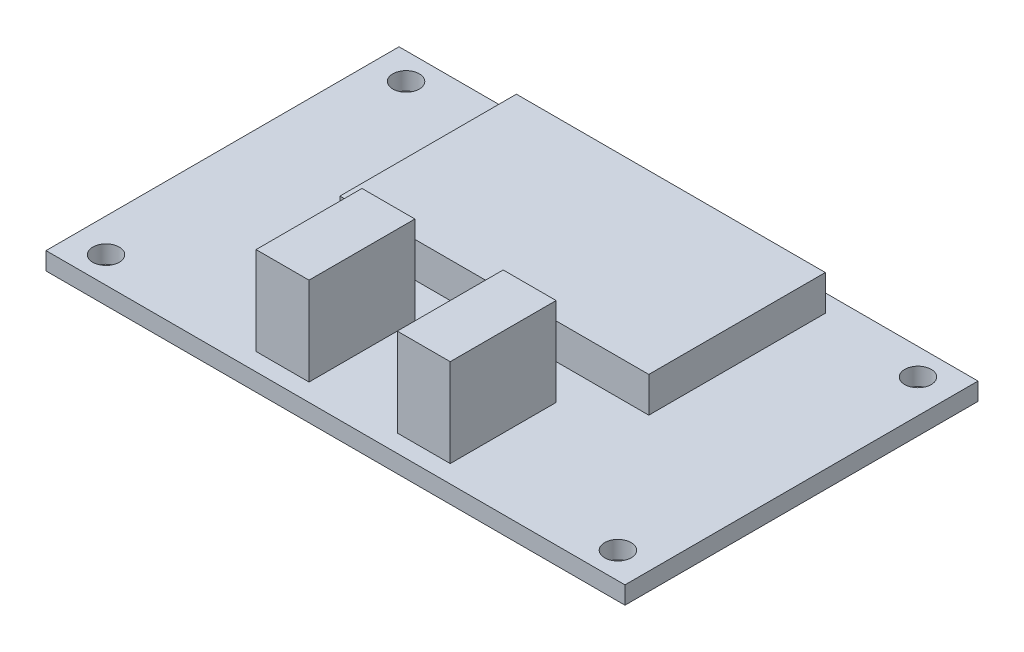
SolidWorks part; units mm, degrees
ref_plane "Front" through (0, 0, 0) normal (0, 0, 1) x (1, 0, 0)
ref_plane "Top" through (0, 0, 0) normal (0, 1, 0) x (1, 0, 0)
ref_plane "Right" through (0, 0, 0) normal (1, 0, 0) x (0, 0, -1)
sketch "Sketch1" plane through (0, 0, 0) normal (0, 1, 0) x (1, 0, 0)
  line L1 (-32.8, -20) -> (32.8, -20)
  line L2 (-32.8, -20) -> (-32.8, 20)
  line L3 (-32.8, 20) -> (32.8, 20)
  line L4 (32.8, -20) -> (32.8, 20)
  line L5 (-32.8, -20) -> (32.8, 20) construction
  line L6 (-32.8, 20) -> (32.8, -20) construction
  point P0 (0, 0)
  dimension "D1" = 65.6
  dimension "D2" = 40
extrude "Boss-Extrude1" add sketch "Sketch1" along normal blind 2
sketch "Sketch2" plane through (0, 2, 0) normal (0, 1, 0) x (1, 0, 0)
  line L1 (-29, -17) -> (29, -17) construction
  line L2 (-29, -17) -> (-29, 17) construction
  line L3 (-29, 17) -> (29, 17) construction
  line L4 (29, -17) -> (29, 17) construction
  line L5 (-29, -17) -> (29, 17) construction
  line L6 (-29, 17) -> (29, -17) construction
  circle A0 centre (-29, 17) radius 1.5
  circle A1 centre (29, 17) radius 1.5
  circle A2 centre (29, -17) radius 1.5
  circle A3 centre (-29, -17) radius 1.5
  point P0 (0, 0)
  dimension "D3" = 3
  dimension "D1" = 58
  dimension "D2" = 34
extrude "Cut-Extrude1" cut sketch "Sketch2" against normal through all
sketch "Sketch3" plane through (0, 2, 0) normal (0, 1, 0) x (1, 0, 0)
  line L0 (32.8, 20) -> (-32.8, 20) construction
  line L1 (-17.5, -2) -> (17.5, -2)
  line L2 (-17.5, -2) -> (-17.5, 18)
  line L3 (-17.5, 18) -> (17.5, 18)
  line L4 (17.5, -2) -> (17.5, 18)
  line L5 (-17.5, -2) -> (17.5, 18) construction
  line L6 (-17.5, 18) -> (17.5, -2) construction
  line L7 (0, 8) -> (0, 0) construction
  point P0 (0, 8)
  dimension "D1" = 20
  dimension "D2" = 35
  dimension "D3" = 2
extrude "Boss-Extrude2" add sketch "Sketch3" along normal blind 4
sketch "Sketch4" plane through (0, 2, 0) normal (0, 1, 0) x (1, 0, 0)
  line L0 (-32.8, -20) -> (32.8, -20) construction
  line L1 (-11, -18) -> (-5, -18)
  line L2 (-11, -18) -> (-11, -6)
  line L3 (-11, -6) -> (-5, -6)
  line L4 (-5, -18) -> (-5, -6)
  line L5 (-11, -18) -> (-5, -6) construction
  line L6 (-11, -6) -> (-5, -18) construction
  line L7 (5, -18) -> (11, -18)
  line L8 (5, -18) -> (5, -6)
  line L9 (5, -6) -> (11, -6)
  line L10 (11, -18) -> (11, -6)
  line L11 (5, -18) -> (11, -6) construction
  line L12 (5, -6) -> (11, -18) construction
  point P0 (-8, -12)
  point P5 (8, -12)
  point P12 (0, -20)
  dimension "D1" = 12
  dimension "D2" = 2
  dimension "D3" = 6
  dimension "D4" = 8
  dimension "D5" = 8
extrude "Boss-Extrude3" add sketch "Sketch4" along normal blind 10
